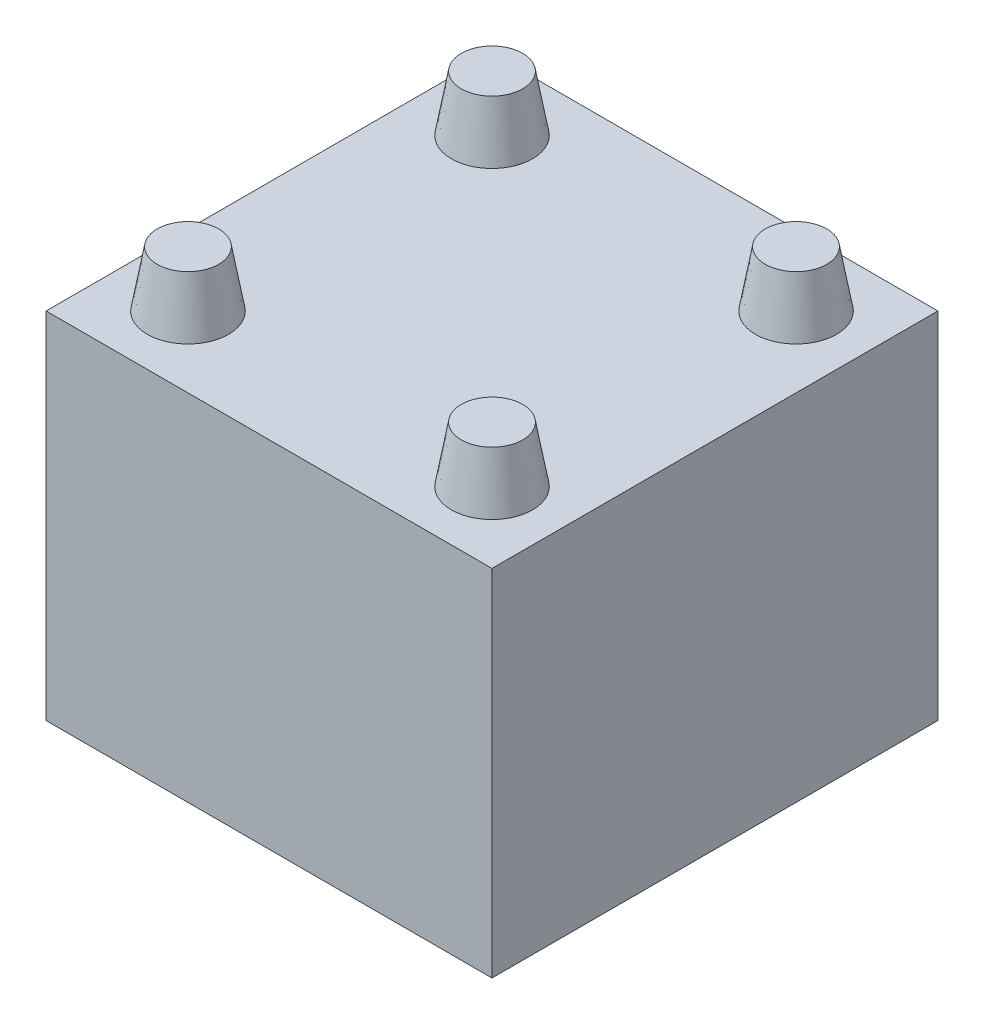
SolidWorks part; units mm, degrees
ref_plane "Front Plane" through (0, 0, 0) normal (0, 0, 1) x (1, 0, 0)
ref_plane "Top Plane" through (0, 0, 0) normal (0, 1, 0) x (1, 0, 0)
ref_plane "Right Plane" through (0, 0, 0) normal (1, 0, 0) x (0, 0, -1)
sketch "Sketch1" plane through (0, 0, 0) normal (0, 1, 0) x (1, 0, 0)
  line L0 (11, 0) -> (-11, 0) construction
  line L1 (-11, -11) -> (11, -11)
  line L2 (-11, -11) -> (-11, 11)
  line L3 (-11, 11) -> (11, 11)
  line L4 (11, -11) -> (11, 11)
  point P7 (0, 0)
  dimension "D1" = 22
extrude "Boss-Extrude1" add sketch "Sketch1" along normal blind 3
sketch "Sketch2" plane through (0, 3, 0) normal (0, 1, 0) x (1, 0, 0)
  line L0 (-7.5, -7.5) -> (7.5, 7.5) construction
  line L1 (7.5, 7.5) -> (-7.5, 7.5) construction
  line L2 (-7.5, 7.5) -> (-7.5, -7.5) construction
  line L3 (-7.5, -7.5) -> (7.5, -7.5) construction
  line L4 (7.5, -7.5) -> (7.5, 7.5) construction
  circle A0 centre (-7.5, 7.5) radius 2
  circle A1 centre (7.5, 7.5) radius 2
  circle A2 centre (7.5, -7.5) radius 2
  circle A3 centre (-7.5, -7.5) radius 2
  point P3 (0, 0)
  dimension "D2" = 4
  dimension "D1" = 15
extrude "Boss-Extrude2" add sketch "Sketch2" along normal blind 14.5
sketch "Sketch3" plane through (0, 17.5, 0) normal (0, 1, 0) x (1, 0, 0)
  circle A0 centre (7.5, -7.5) radius 2 construction
  circle A1 centre (7.5, 7.5) radius 2 construction
  circle A2 centre (-7.5, 7.5) radius 2 construction
  circle A3 centre (-7.5, -7.5) radius 2 construction
  circle A4 centre (7.5, -7.5) radius 2
  circle A5 centre (7.5, 7.5) radius 2
  circle A6 centre (-7.5, 7.5) radius 2
  circle A7 centre (-7.5, -7.5) radius 2
extrude "Boss-Extrude3" add sketch "Sketch3" along normal blind 2.75 draft 10
sketch "Sketch4" plane through (0, 3, 0) normal (0, 1, 0) x (1, 0, 0)
  line L5 (-7.2172, -7.7828) -> (7.7828, 7.2172)
  line L6 (-7.2172, -7.7828) -> (-7.7828, -7.2172)
  line L7 (-7.7828, -7.2172) -> (7.2172, 7.7828)
  line L8 (7.7828, 7.2172) -> (7.2172, 7.7828)
  circle A4 centre (-7.5, -7.5) radius 1.5151 construction
  circle A5 centre (7.5, 7.5) radius 1.5151 construction
  point P7 (-7.5, -7.5)
  point P11 (7.5, 7.5)
  dimension "D1" = 0.8
extrude "Boss-Extrude4" add sketch "Sketch4" along normal offset from surface (14.5 mm away) 2.75 up to face at (-7.5, 20.25, 9.0151)
sketch "Sketch5" plane through (0, 3, 0) normal (0, 1, 0) x (1, 0, 0)
  line L1 (-7.2172, 7.7828) -> (7.7828, -7.2172)
  line L2 (-7.2172, 7.7828) -> (-7.7828, 7.2172)
  line L3 (-7.7828, 7.2172) -> (7.2172, -7.7828)
  line L4 (7.7828, -7.2172) -> (7.2172, -7.7828)
  circle A0 centre (7.5, -7.5) radius 1.5151 construction
  circle A1 centre (-7.5, 7.5) radius 1.5151 construction
  point P4 (7.5, -7.5)
  point P7 (-7.5, 7.5)
  dimension "D1" = 0.8
extrude "Boss-Extrude5" add sketch "Sketch5" along normal offset from surface (14.5 mm away) 2.75 up to face at (-7.5, 20.25, -5.9849)
sketch "Sketch6" plane through (0, 3, 0) normal (0, 1, 0) x (1, 0, 0)
  line L4 (-11, 11) -> (-11, -11)
  line L5 (-11, -11) -> (11, -11)
  line L6 (11, -11) -> (11, 11)
  line L7 (11, 11) -> (-11, 11)
  line L8 (-11, 11) -> (-11, -11)
  line L9 (-11, -11) -> (11, -11)
  line L10 (11, -11) -> (11, 11)
  line L11 (11, 11) -> (-11, 11)
  dimension "D1" = 0
extrude "Boss-Extrude6" add sketch "Sketch6" along normal up to surface (14.5 mm away) up to face at (0, 17.5, 0)
